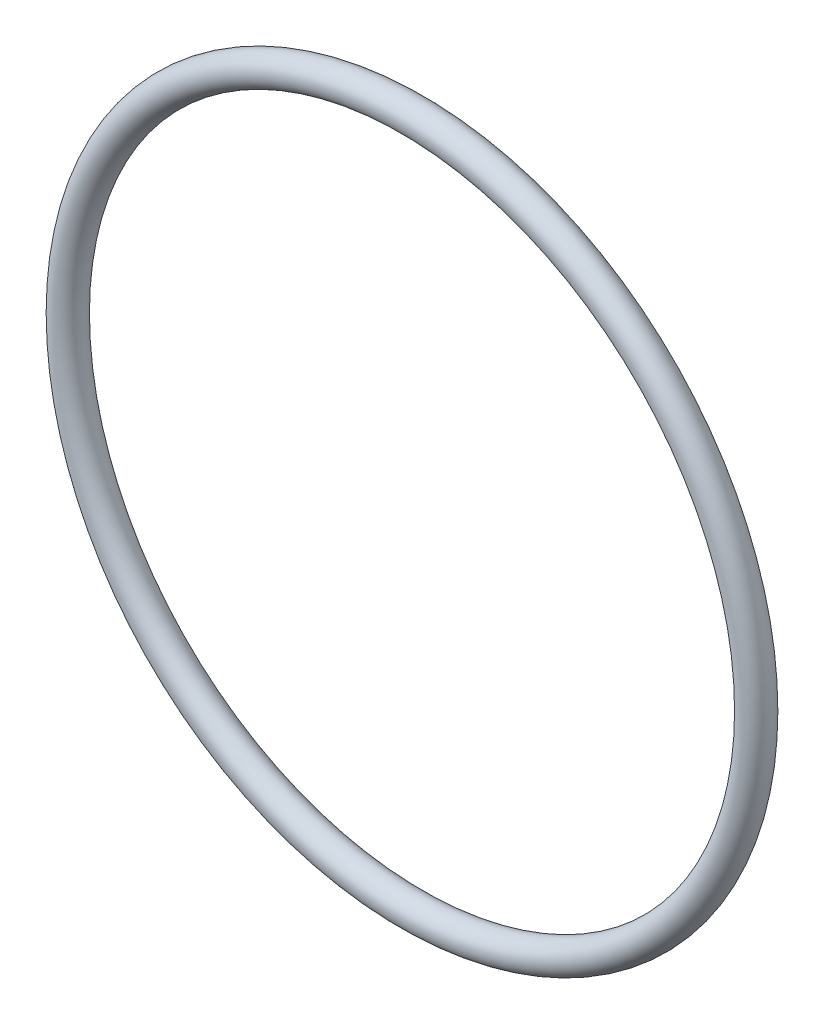
SolidWorks part; units mm, degrees
ref_plane "Front" through (0, 0, 0) normal (0, 0, 1) x (1, 0, 0)
ref_plane "Top" through (0, 0, 0) normal (0, 1, 0) x (1, 0, 0)
ref_plane "Right" through (0, 0, 0) normal (1, 0, 0) x (0, 0, -1)
sketch "Sketch1" plane through (0, 0, 0) normal (1, 0, 0) x (0, -1, 0)
  line L0 (0, -1.7653) -> (0, 1.7653) construction
  line L2 (-45.5701, 0) -> (45.5701, 0) construction
  line L3 (-37.8968, 0) -> (37.8968, 0) construction
  circle A0 centre (39.6621, 0) radius 1.7653
  point P9 (37.8968, 0)
  point P10 (41.4274, 0)
  point P13 (39.6621, 1.7653)
  point P14 (39.6621, -1.7653)
  dimension "Width" = 3.5306
  dimension "ID" = 75.7936
revolve "Revolve1" add sketch "Sketch1" angle 360 about L0
